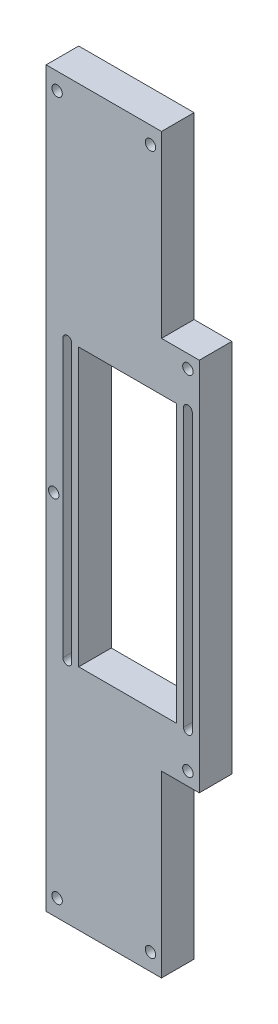
SolidWorks part; units mm, degrees
ref_plane "Front Plane" through (0, 0, 0) normal (0, 0, 1) x (1, 0, 0)
ref_plane "Top Plane" through (0, 0, 0) normal (0, 1, 0) x (1, 0, 0)
ref_plane "Right Plane" through (0, 0, 0) normal (1, 0, 0) x (0, 0, -1)
sketch "Sketch4" plane through (0, 0, 0) normal (0, 0, 1) x (1, 0, 0)
  line L0 (-109.5445, 259.9527) -> (-109.5445, 34.9527)
  line L2 (-109.5445, 34.9527) -> (-74.1404, 34.9527)
  line L3 (-74.1404, 34.9527) -> (-74.1404, 89.9527)
  line L4 (-74.1404, 89.9527) -> (-62.5445, 89.9527)
  line L5 (-62.5445, 89.9527) -> (-62.5445, 204.9527)
  line L8 (-99.5445, 189.9527) -> (-99.5445, 104.9527)
  line L9 (-99.5445, 189.9527) -> (-99.5445, 104.9527) construction
  line L10 (-99.5445, 104.9527) -> (-69.5445, 104.9527)
  line L11 (-69.5445, 104.9527) -> (-69.5445, 189.9527)
  line L12 (-69.5445, 104.9527) -> (-69.5445, 189.9527) construction
  line L13 (-103.0445, 104.9527) -> (-103.0445, 147.4527) construction
  line L14 (-104.3945, 104.9527) -> (-104.3945, 147.4527)
  line L15 (-101.6945, 104.9527) -> (-101.6945, 147.4527)
  line L16 (-66.0445, 104.9527) -> (-66.0445, 147.4527) construction
  line L17 (-67.3945, 104.9527) -> (-67.3945, 147.4527)
  line L18 (-64.6945, 104.9527) -> (-64.6945, 147.4527)
  line L20 (-99.5445, 189.9527) -> (-69.5445, 189.9527)
  line L21 (-74.1404, 204.9527) -> (-62.5445, 204.9527)
  line L22 (-74.1404, 259.9527) -> (-74.1404, 204.9527)
  line L23 (-109.5445, 259.9527) -> (-74.1404, 259.9527)
  line L24 (-66.0445, 189.9527) -> (-66.0445, 147.4527) construction
  line L25 (-67.3945, 189.9527) -> (-67.3945, 147.4527)
  line L26 (-64.6945, 189.9527) -> (-64.6945, 147.4527)
  line L27 (-103.0445, 189.9527) -> (-103.0445, 147.4527) construction
  line L28 (-104.3945, 189.9527) -> (-104.3945, 147.4527)
  line L29 (-101.6945, 189.9527) -> (-101.6945, 147.4527)
  circle A0 centre (-106.1787, 40.1814) radius 1.6
  circle A1 centre (-77.5193, 40.1814) radius 1.6
  circle A2 centre (-66.0445, 94.0197) radius 1.6
  circle A3 centre (-107.2098, 147.4527) radius 1.6
  arc A4 (-104.3945, 104.9527) -> (-101.6945, 104.9527) centre (-103.0445, 104.9527) ccw
  arc A5 (-101.6945, 147.4527) -> (-104.3945, 147.4527) centre (-103.0445, 147.4527) ccw
  arc A6 (-67.3945, 104.9527) -> (-64.6945, 104.9527) centre (-66.0445, 104.9527) ccw
  arc A7 (-64.6945, 147.4527) -> (-67.3945, 147.4527) centre (-66.0445, 147.4527) ccw
  circle A8 centre (-66.0445, 200.8856) radius 1.6
  circle A9 centre (-77.5193, 254.724) radius 1.6
  circle A10 centre (-106.1787, 254.724) radius 1.6
  arc A11 (-67.3945, 189.9527) -> (-64.6945, 189.9527) centre (-66.0445, 189.9527) cw
  arc A12 (-64.6945, 147.4527) -> (-67.3945, 147.4527) centre (-66.0445, 147.4527) cw
  arc A13 (-104.3945, 189.9527) -> (-101.6945, 189.9527) centre (-103.0445, 189.9527) cw
  arc A14 (-101.6945, 147.4527) -> (-104.3945, 147.4527) centre (-103.0445, 147.4527) cw
  point P38 (-103.0445, 126.2027)
  point P43 (-66.0445, 126.2027)
  point P59 (-69.5445, 147.4527)
  point P60 (-99.5445, 147.4527)
  point P66 (-66.0445, 168.7027)
  point P73 (-103.0445, 168.7027)
  dimension "D1" = 225
  dimension "D2" = 115
extrude "Boss-Extrude6" add sketch "Sketch4" along normal blind 10 contours L23 L0 L2 L3 L4 L5 L21 L22 A9 L8 L20 L11 L10 A0 A1 A2 A3 A8 A10 L25 A11 L26 L18 A6 L17 L28 A13 L29 L15 A4 L14
